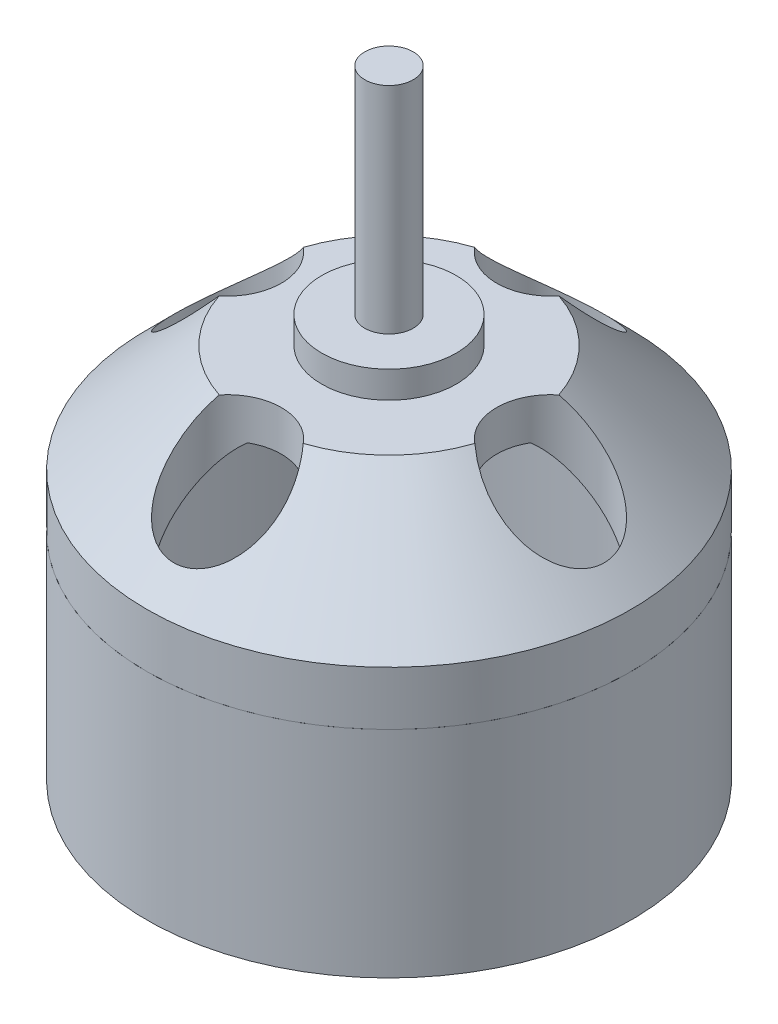
SolidWorks part; units mm, degrees
ref_plane "Ön Düzlem" through (0, 0, 0) normal (0, 0, 1) x (1, 0, 0)
ref_plane "Üst Düzlem" through (0, 0, 0) normal (0, 1, 0) x (1, 0, 0)
ref_plane "Sağ Düzlem" through (0, 0, 0) normal (1, 0, 0) x (0, 0, -1)
sketch "Çizim2" plane through (0, 0, 0) normal (0, 1, 0) x (1, 0, 0)
  circle A0 centre (0, 0) radius 9
  dimension "D1" = 18
extrude "Yükseklik-Ekstrüzyon1" add sketch "Çizim2" along normal blind 1
sketch "Çizim3" plane through (0, 1, 0) normal (0, 1, 0) x (1, 0, 0)
  circle A1 centre (0, 0) radius 9
  circle A2 centre (0, 0) radius 9
  dimension "D1" = 0
extrude "Yükseklik-Ekstrüzyon2" add sketch "Çizim3" along normal blind 5
chamfer "Pah1" distance 4 angle 45 1 edges at (0, 6, 9)
shell "İç Boşaltma1" thickness 1.5
sketch "Çizim5" plane through (0, 6, 0) normal (0, 1, 0) x (1, 0, 0)
  circle A0 centre (0, -6) radius 2
  circle A1 centre (-6, 0) radius 2
  circle A2 centre (0, 6) radius 2
  circle A3 centre (6, 0) radius 2
  point P12 (0, 0)
  dimension "D2" = 4
  dimension "D1" = 6
  dimension "D3" = 4
extrude "Kes-Ekstrüzyon1" cut sketch "Çizim5" against normal blind 6
sketch "Çizim6" plane through (0, 0, 0) normal (0, -1, 0) x (1, 0, 0)
  circle A0 centre (0, 0) radius 9
  circle A1 centre (0, 0) radius 8.5
  dimension "D1" = 17
  dimension "D2" = 18
sketch "Çizim7" plane through (0, 6, 0) normal (0, 1, 0) x (1, 0, 0)
  circle A0 centre (0, 0) radius 2.5
  dimension "D1" = 5
extrude "Yükseklik-Ekstrüzyon4" add sketch "Çizim7" along normal blind 1
sketch "Çizim8" plane through (0, 7, 0) normal (0, 1, 0) x (1, 0, 0)
  circle A0 centre (0, 0) radius 0.9
  dimension "D1" = 1.8
extrude "Yükseklik-Ekstrüzyon6" add sketch "Çizim6" along normal blind 8 separate body contours A0
extrude "Yükseklik-Ekstrüzyon7" add sketch "Çizim8" along normal blind 8 and the other way blind 20 separate body
